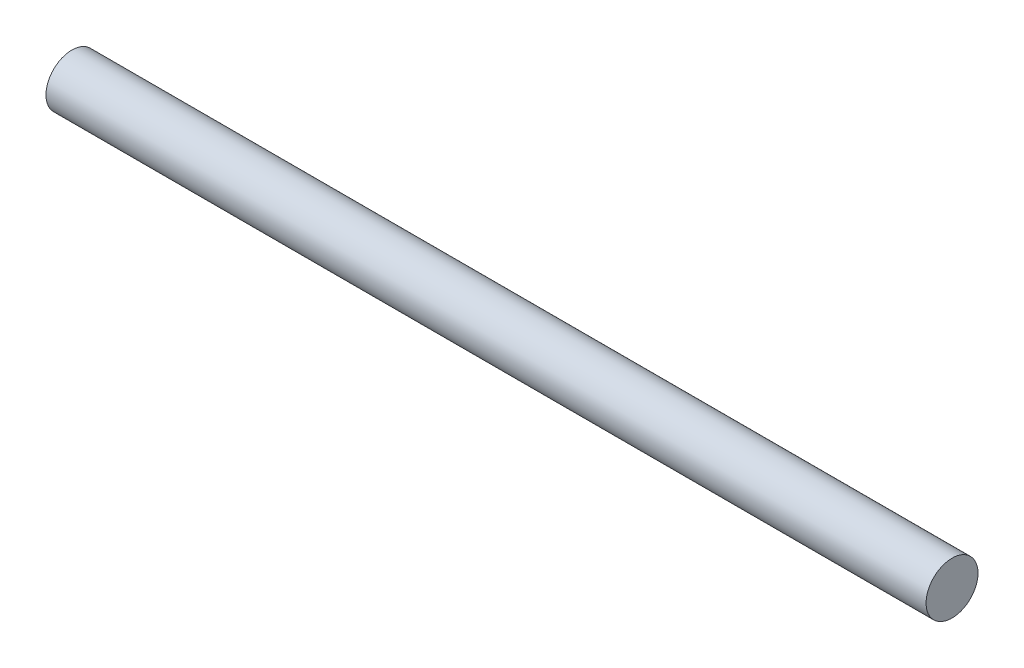
SolidWorks part; units mm, degrees
ref_plane "Front Plane" through (0, 0, 0) normal (0, 0, 1) x (1, 0, 0)
ref_plane "Top Plane" through (0, 0, 0) normal (0, 1, 0) x (1, 0, 0)
ref_plane "Right Plane" through (0, 0, 0) normal (1, 0, 0) x (0, 0, -1)
sketch "Sketch1" plane through (0, 0, 0) normal (1, 0, 0) x (0, 0, -1)
  circle A0 centre (0, 0) radius 1.475
  dimension "D1" = 2.95
extrude "Boss-Extrude1" add sketch "Sketch1" along normal blind 50
